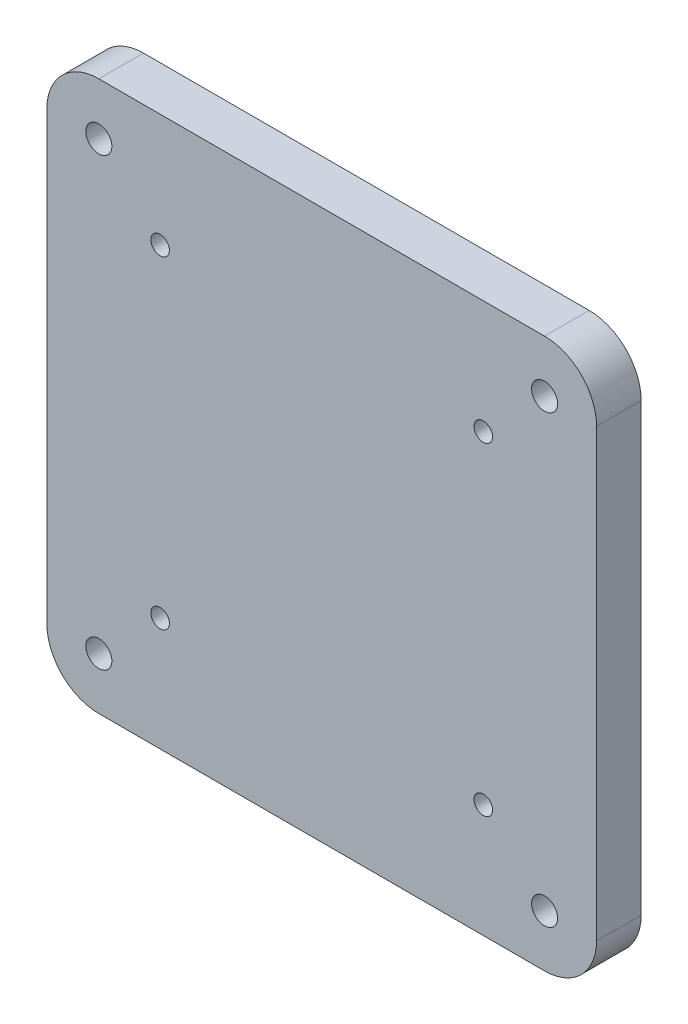
SolidWorks part; units mm, degrees
ref_plane "Plan de face" through (0, 0, 0) normal (0, 0, 1) x (1, 0, 0)
ref_plane "Plan de dessus" through (0, 0, 0) normal (0, 1, 0) x (1, 0, 0)
ref_plane "Plan de droite" through (0, 0, 0) normal (1, 0, 0) x (0, 0, -1)
sketch "Esquisse1" plane through (0, 0, 0) normal (0, 0, 1) x (1, 0, 0)
  line L1 (-37, 37) -> (37, 37)
  line L2 (-37, 37) -> (-37, -37)
  line L7 (-37, -37) -> (37, -37)
  line L8 (37, 37) -> (37, -37)
  line L13 (-30, 30) -> (30, 30) construction
  line L15 (-30, 30) -> (-30, -30) construction
  line L16 (-30, -30) -> (30, -30) construction
  line L17 (30, 30) -> (30, -30) construction
  line L18 (-21.75, 21.75) -> (21.75, 21.75) construction
  line L19 (-21.75, 21.75) -> (-21.75, -21.75) construction
  line L20 (-21.75, -21.75) -> (21.75, -21.75) construction
  line L21 (21.75, 21.75) -> (21.75, -21.75) construction
  circle A12 centre (-30, 30) radius 1.75
  circle A13 centre (-21.75, 21.75) radius 1.25
  circle A14 centre (30, 30) radius 1.75
  circle A15 centre (21.75, 21.75) radius 1.25
  circle A16 centre (21.75, -21.75) radius 1.25
  circle A17 centre (-21.75, -21.75) radius 1.25
  circle A18 centre (-30, -30) radius 1.75
  circle A19 centre (30, -30) radius 1.75
  point P13 (0, 21.75)
  point P14 (0, 30)
  point P15 (0, 37)
  point P16 (37, 0)
  point P17 (-30, 0)
  point P18 (-21.75, 0)
  point P28 (0, 0)
  dimension "D2" = 43.5
  dimension "D4" = 3.5
  dimension "D5" = 2.5
  dimension "D1" = 60
  dimension "D3" = 7
extrude "Boss.-Extru.1" add sketch "Esquisse1" along normal blind 6
fillet "Congé1" radius 7 4 edges at (37, 37, 3) (37, -37, 3) (-37, -37, 3) (-37, 37, 3)
